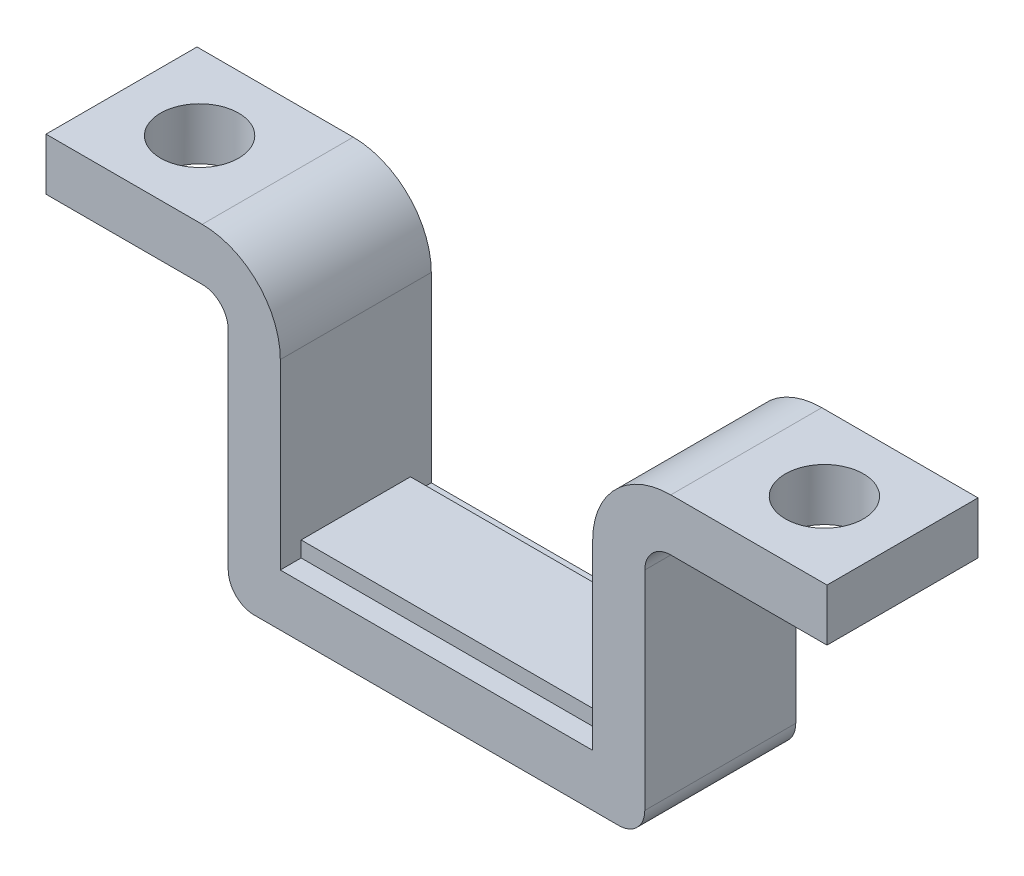
SolidWorks part; units mm, degrees
ref_plane "Front Plane" through (0, 0, 0) normal (0, 0, 1) x (1, 0, 0)
ref_plane "Top Plane" through (0, 0, 0) normal (0, 1, 0) x (1, 0, 0)
ref_plane "Right Plane" through (0, 0, 0) normal (1, 0, 0) x (0, 0, -1)
sketch "Sketch2" plane through (0, 0, 0) normal (0, 0, 1) x (1, 0, 0)
  line L1 (-5, 5) -> (5, 5)
  line L2 (-6, 4) -> (-6, -4)
  line L3 (-5, -5) -> (5, -5)
  line L4 (6, 4) -> (6, -4)
  arc A0 (-6, -4) -> (-5, -5) centre (-5, -4) ccw
  arc A1 (5, -5) -> (6, -4) centre (5, -4) ccw
  arc A2 (6, 4) -> (5, 5) centre (5, 4) ccw
  arc A3 (-6, 4) -> (-5, 5) centre (-5, 4) cw
  circle A4 centre (-4.5, 0) radius 0.8
  circle A5 centre (4.5, 0) radius 0.8
  circle A6 centre (0, 0) radius 2
  point P4 (0, 5)
  point P6 (6, 0)
  dimension "D1" = 1
  dimension "D6" = 1.6
  dimension "D7" = 4
  dimension "D2" = 12
  dimension "D3" = 10
  dimension "D4" = 4.5
  dimension "D5" = 4.5
sketch "Sketch3" plane through (0, 0, 0) normal (0, 0, 1) x (1, 0, 0)
  line L0 (-6, -5) -> (6, -5)
  line L1 (6, -5) -> (6, 2)
  line L2 (-6, -5) -> (-6, 2)
  line L3 (-5, -5) -> (5, -5) construction
  line L4 (-6, 4) -> (-6, -4) construction
  line L5 (8, -6) -> (8, 2)
  line L6 (-7, -7) -> (7, -7)
  line L7 (-8, -6) -> (-8, 2)
  line L8 (-8, -7) -> (-8, 5.1614) construction
  line L9 (-9, 3) -> (-15, 3)
  line L10 (-15, 3) -> (-15, 5)
  line L11 (-15, 5) -> (-9, 5)
  line L12 (-6, -5) -> (-6, 5.1614) construction
  line L13 (-5, 5) -> (5, 5) construction
  line L14 (8, -7) -> (8, 5.1614) construction
  line L15 (9, 5) -> (15, 5)
  line L16 (15, 5) -> (15, 3)
  line L17 (15, 3) -> (9, 3)
  line L18 (6, -5) -> (6, 5.1614) construction
  line L19 (-8, -7) -> (8, -7) construction
  arc A0 (-8, 2) -> (-9, 3) centre (-9, 2) ccw
  arc A1 (-6, 2) -> (-9, 5) centre (-9, 2) ccw
  arc A2 (9, 3) -> (8, 2) centre (9, 2) ccw
  arc A3 (9, 5) -> (6, 2) centre (9, 2) ccw
  arc A4 (-7, -7) -> (-8, -6) centre (-7, -6) cw
  arc A5 (8, -6) -> (7, -7) centre (7, -6) cw
  point P6 (0, -5)
  point P7 (0, -5)
  dimension "D3" = 1
  dimension "D4" = 3
  dimension "D6" = 1
  dimension "D7" = 3
  dimension "D10" = 1
  dimension "D11" = 1
  dimension "D2" = 2
  dimension "D5" = 6
  dimension "D8" = 2
  dimension "D9" = 6
  dimension "D1" = 2
extrude "Boss-Extrude1" add sketch "Sketch3" along normal mid plane 5.8
sketch "Sketch4" plane through (0, 0, 0) normal (0, 0, 1) x (1, 0, 0)
  line L0 (-6, -5) -> (-6, -4.4)
  line L1 (-6, 4) -> (-6, -4) construction
  line L2 (-6, -4.4) -> (6, -4.4)
  line L3 (6, 4) -> (6, -4) construction
  line L4 (6, -4.4) -> (6, -5)
  line L5 (-5, -5) -> (5, -5) construction
  line L6 (-6, -5) -> (6, -5)
  dimension "D1" = 0.6
extrude "Boss-Extrude2" add sketch "Sketch4" along normal mid plane 4.2
sketch "Sketch5" plane through (0, 5, 0) normal (0, 1, 0) x (1, 0, 0)
  line L0 (-9, 2.9) -> (-15, 2.9) construction
  line L1 (15, 2.9) -> (9, 2.9) construction
  circle A0 centre (12, 0) radius 1.5
  circle A1 centre (-12, 0) radius 1.5
  point P9 (-12, 2.9)
  point P12 (12, 2.9)
  dimension "D1" = 3
  dimension "D2" = 3
extrude "Cut-Extrude1" cut sketch "Sketch5" against normal through all
equation "\"D9@Sketch3\"=\"D5@Sketch3\""
